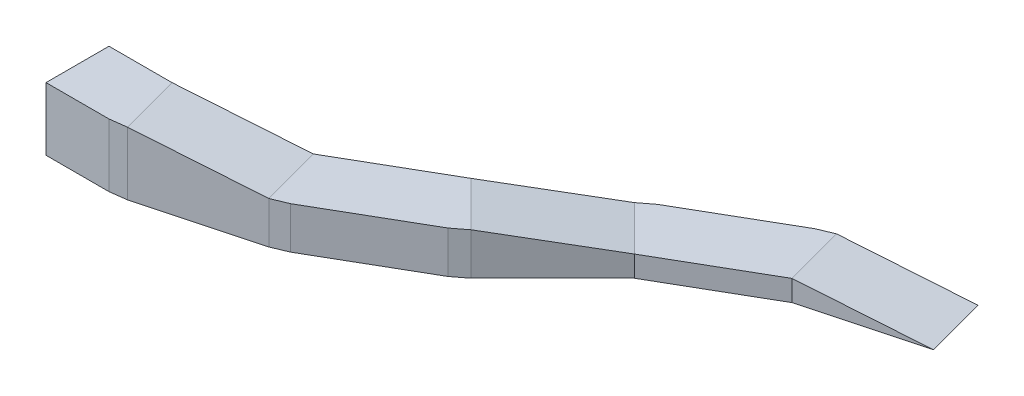
SolidWorks part; units mm, degrees
ref_plane "Front Plane" through (0, 0, 0) normal (0, 0, 1) x (1, 0, 0)
ref_plane "Top Plane" through (0, 0, 0) normal (0, 1, 0) x (1, 0, 0)
ref_plane "Right Plane" through (0, 0, 0) normal (1, 0, 0) x (0, 0, -1)
sketch "Sketch1" plane through (0, 0, 0) normal (0, 1, 0) x (1, 0, 0)
  line L0 (0, 0) -> (-1000, 0)
  line L1 (0, 0) -> (0, 600)
  line L2 (0, 600) -> (-1000, 600)
  line L3 (-1000, 0) -> (-2062.5184, -284.7009)
  line L4 (-2062.5184, -284.7009) -> (-3015.1464, -834.7009)
  line L5 (-1155.2914, 579.5555) -> (-2217.8098, 294.8545)
  line L6 (-1000, 600) -> (-1155.2914, 579.5555)
  line L7 (-3015.1464, -834.7009) -> (-3792.9638, -1612.5184)
  line L8 (-2217.8098, 294.8545) -> (-2362.5184, 234.9143)
  line L9 (-2362.5184, 234.9143) -> (-3315.1464, -315.0857)
  line L11 (-3439.4104, -410.4369) -> (-4217.2279, -1188.2543)
  line L12 (-3315.1464, -315.0857) -> (-3439.4104, -410.4369)
  line L26 (-7232.3742, -2022.9553) -> (-6232.3742, -2022.9553)
  line L27 (-7232.3742, -2022.9553) -> (-7232.3742, -2622.9553)
  line L28 (-7232.3742, -2622.9553) -> (-6232.3742, -2622.9553)
  line L29 (-6232.3742, -2022.9553) -> (-5169.8558, -1738.2543)
  line L30 (-5169.8558, -1738.2543) -> (-4217.2279, -1188.2543)
  line L31 (-6077.0828, -2602.5108) -> (-5014.5644, -2317.8098)
  line L32 (-6232.3742, -2622.9553) -> (-6077.0828, -2602.5108)
  line L34 (-5014.5644, -2317.8098) -> (-4869.8558, -2257.8696)
  line L35 (-4869.8558, -2257.8696) -> (-3917.2279, -1707.8696)
  line L37 (-3917.2279, -1707.8696) -> (-3792.9638, -1612.5184)
extrude "Boss-Extrude1" add sketch "Sketch1" against normal blind 600
sketch "Sketch9" plane through (0, 0, 0) normal (0, 1, 0) x (1, 0, 0)
  line L0 (-1000, 0) -> (0, 0)
  line L1 (0, 0) -> (0, 600)
  line L2 (0, 600) -> (-1000, 600)
  line L3 (-1000, 600) -> (-1155.2914, 579.5555)
  line L4 (-1155.2914, 579.5555) -> (-1000, 0)
extrude "Cut-Extrude1" cut sketch "Sketch9" against normal blind 600
sketch "Sketch10" plane through (-66.9873, 0, -250) normal (0.2588, 0, 0.9659) x (0.9659, 0, -0.2588)
  line L2 (-2065.9258, -600) -> (-2065.9258, 0) construction
  line L3 (-2065.9258, -400) -> (-965.9258, -600)
  line L4 (-965.9258, -600) -> (-965.9258, 0)
  line L5 (-965.9258, 0) -> (-2065.9258, 0)
  line L6 (-2065.9258, 0) -> (-2065.9258, -400)
extrude "Cut-Extrude2" cut sketch "Sketch10" against normal blind 600
sketch "Sketch11" plane through (0, 0, 0) normal (0, 1, 0) x (1, 0, 0)
  line L0 (-2062.5184, -284.7009) -> (-3015.1464, -834.7009)
  line L1 (-3015.1464, -834.7009) -> (-3439.4104, -410.4369)
  line L2 (-3439.4104, -410.4369) -> (-3315.1464, -315.0857)
  line L3 (-3315.1464, -315.0857) -> (-2362.5184, 234.9143)
  line L4 (-2362.5184, 234.9143) -> (-2217.8098, 294.8545)
  line L5 (-2217.8098, 294.8545) -> (-2062.5184, -284.7009)
extrude "Cut-Extrude3" cut sketch "Sketch11" against normal blind 400
sketch "Sketch12" plane through (-1090.2227, 0, -1090.2227) normal (0.7071, 0, 0.7071) x (0.7071, 0, -0.7071)
  line L0 (-3822.2531, -200) -> (-3822.2531, 0)
  line L1 (-3822.2531, -600) -> (-3822.2531, 0) construction
  line L2 (-3822.2531, -200) -> (-2722.2531, -400)
  line L3 (-2722.2531, -400) -> (-2722.2531, 0)
  line L4 (-2722.2531, 0) -> (-3822.2531, 0)
extrude "Cut-Extrude4" cut sketch "Sketch12" against normal blind 600
sketch "Sketch13" plane through (0, 0, 0) normal (0, 1, 0) x (1, 0, 0)
  line L0 (-4217.2279, -1188.2543) -> (-3792.9638, -1612.5184)
  line L1 (-3792.9638, -1612.5184) -> (-3917.2279, -1707.8696)
  line L2 (-3917.2279, -1707.8696) -> (-4869.8558, -2257.8696)
  line L3 (-4869.8558, -2257.8696) -> (-5014.5644, -2317.8098)
  line L4 (-5014.5644, -2317.8098) -> (-5169.8558, -1738.2543)
  line L5 (-5169.8558, -1738.2543) -> (-4217.2279, -1188.2543)
extrude "Cut-Extrude5" cut sketch "Sketch13" against normal blind 200
sketch "Sketch14" plane through (243.5403, 0, 908.9049) normal (0.2588, 0, 0.9659) x (0.9659, 0, -0.2588)
  line L0 (-5443.5906, -200) -> (-6543.5906, 0)
  line L1 (-6543.5906, 0) -> (-5443.5906, 0)
  line L2 (-5443.5906, 0) -> (-5443.5906, -200)
extrude "Cut-Extrude6" cut sketch "Sketch14" against normal blind 6000
sketch "Sketch15" plane through (0, 0, 0) normal (0, 1, 0) x (1, 0, 0)
  line L0 (-6232.3742, -2022.9553) -> (-6832.3742, -2022.9553)
  line L1 (-6232.3742, -2022.9553) -> (-7232.3742, -2022.9553) construction
  line L2 (-6832.3742, -2022.9553) -> (-6832.3742, -2622.9553)
  line L3 (-7232.3742, -2622.9553) -> (-6232.3742, -2622.9553) construction
ref_plane "Plane1" through (-6832.3742, 0, 0) normal (1, 0, 0) x (0, 0, -1)
sketch "Sketch16" plane through (-6832.3742, 0, 0) normal (1, 0, 0) x (0, 0, -1)
  line L1 (-3170.3838, 509.4224) -> (-637.4604, 509.4224)
  line L2 (-3170.3838, 509.4224) -> (-3170.3838, -976.4888)
  line L3 (-3170.3838, -976.4888) -> (-637.4604, -976.4888)
  line L4 (-637.4604, 509.4224) -> (-637.4604, -976.4888)
extrude "Cut-Extrude7" cut sketch "Sketch16" against normal blind 1000
